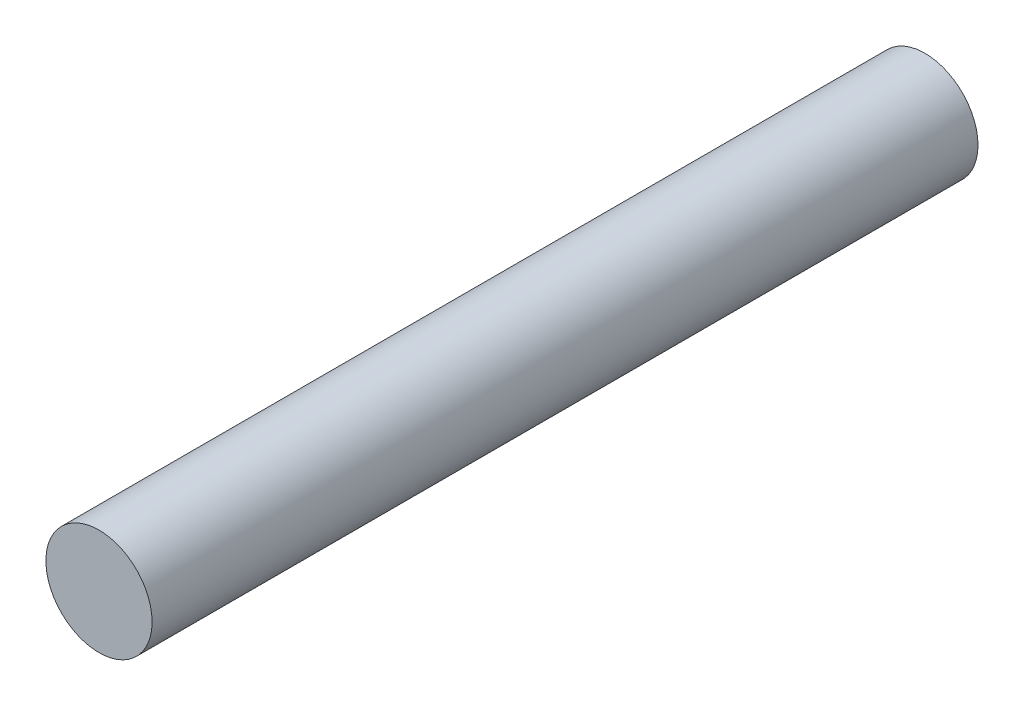
SolidWorks part; units mm, degrees
ref_plane "Alzado" through (0, 0, 0) normal (0, 0, 1) x (1, 0, 0)
ref_plane "Planta" through (0, 0, 0) normal (0, 1, 0) x (1, 0, 0)
ref_plane "Vista lateral" through (0, 0, 0) normal (1, 0, 0) x (0, 0, -1)
sketch "Croquis1" plane through (0, 0, 0) normal (0, 0, 1) x (1, 0, 0)
  circle A0 centre (0, 0) radius 9
  dimension "D1" = 18
extrude "Saliente-Extruir1" add sketch "Croquis1" along normal blind 140
